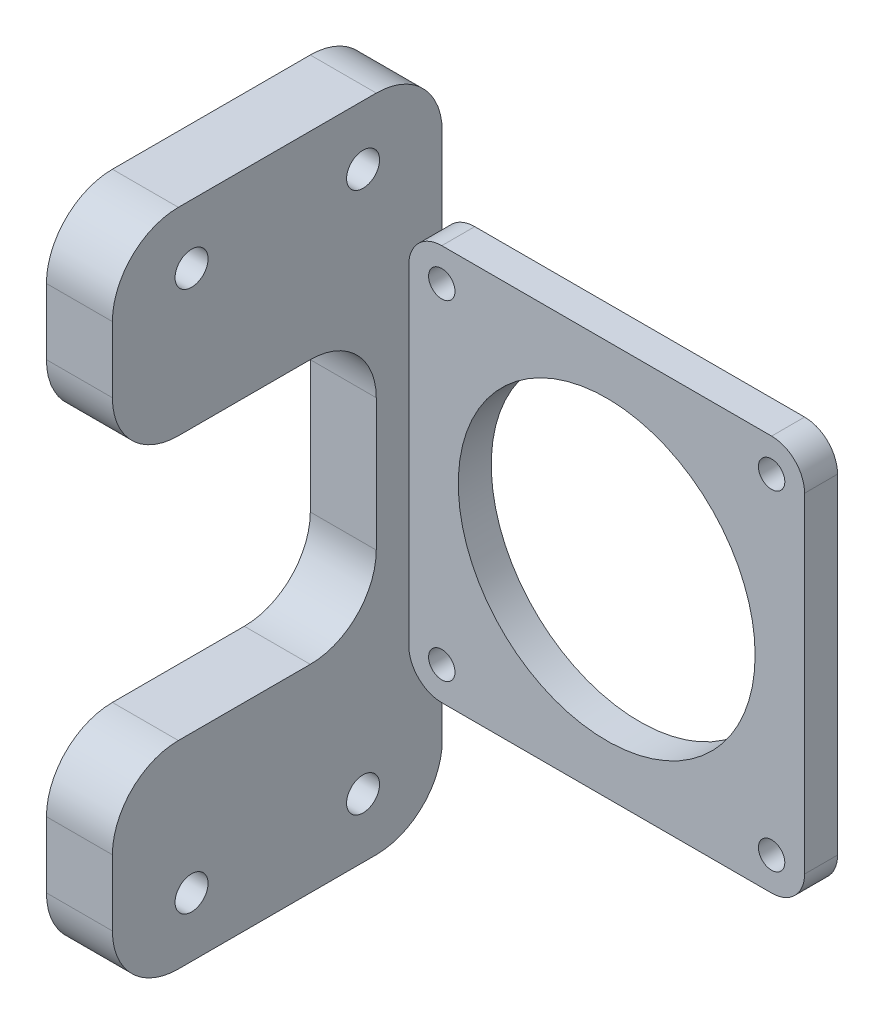
SolidWorks part; units mm, degrees
ref_plane "Front Plane" through (0, 0, 0) normal (0, 0, 1) x (1, 0, 0)
ref_plane "Top Plane" through (0, 0, 0) normal (0, 1, 0) x (1, 0, 0)
ref_plane "Right Plane" through (0, 0, 0) normal (1, 0, 0) x (0, 0, -1)
sketch "Sketch2" plane through (0, 0, 0) normal (0, 0, 1) x (1, 0, 0)
  line L0 (0, 0) -> (0, 35.8787) construction
  line L1 (25, 30) -> (-25, 30)
  line L2 (30, 25) -> (30, -25)
  line L3 (25, -30) -> (-25, -30)
  line L4 (-30, 25) -> (-30, -25)
  line L5 (30, 30) -> (-30, -30) construction
  line L6 (30, -30) -> (-30, 30) construction
  line L7 (-17.179, 0) -> (23.6868, 0) construction
  circle A0 centre (-25, 25) radius 2
  circle A1 centre (25, 25) radius 2
  circle A2 centre (25, -25) radius 2
  circle A3 centre (-25, -25) radius 2
  arc A4 (-25, -30) -> (-30, -25) centre (-25, -25) cw
  arc A5 (30, -25) -> (25, -30) centre (25, -25) cw
  arc A6 (30, 25) -> (25, 30) centre (25, 25) ccw
  arc A7 (-25, 30) -> (-30, 25) centre (-25, 25) ccw
  circle A8 centre (0, 0) radius 22.5
  point P0 (0, 0)
  dimension "D3" = 4
  dimension "D5" = 5
  dimension "D6" = 45
  dimension "D1" = 60
  dimension "D2" = 60
  dimension "D4" = 25
extrude "Boss-Extrude2" add sketch "Sketch2" along normal blind 5
sketch "Sketch3" plane through (-30, 0, 0) normal (-1, 0, 0) x (0, 0, 1)
  line L0 (-22.7369, 0) -> (15.4737, 0) construction
  line L5 (9.9329, 50) -> (39.9329, 50)
  line L6 (-0.0671, 40) -> (-0.0671, -40)
  line L7 (9.9329, -50) -> (39.9329, -50)
  line L8 (49.9329, 40) -> (49.9329, -40)
  line L9 (49.9329, 50) -> (-0.0671, -50) construction
  line L10 (-0.0671, 50) -> (49.9329, -50) construction
  line L11 (24.9329, 0) -> (24.9329, 22.6424) construction
  line L12 (0, 35) -> (68.0193, 35) construction
  line L13 (0, -30) -> (89.451, -30)
  line L14 (19.9329, 20) -> (39.9329, 20)
  line L15 (19.9329, -20) -> (39.9329, -20)
  line L16 (9.9329, 10) -> (9.9329, -10)
  circle A0 centre (11.9329, 41) radius 2.5
  circle A1 centre (37.9329, 41) radius 2.5
  circle A2 centre (37.9329, -41) radius 2.5
  circle A3 centre (11.9329, -41) radius 2.5
  arc A4 (9.9329, -50) -> (-0.0671, -40) centre (9.9329, -40) cw
  arc A5 (39.9329, -50) -> (49.9329, -40) centre (39.9329, -40) ccw
  arc A6 (49.9329, 40) -> (39.9329, 50) centre (39.9329, 40) ccw
  arc A7 (-0.0671, 40) -> (9.9329, 50) centre (9.9329, 40) cw
  arc A8 (49.9329, 30) -> (39.9329, 20) centre (39.9329, 30) cw
  arc A9 (19.9329, -20) -> (9.9329, -10) centre (19.9329, -10) cw
  arc A10 (49.9329, -30) -> (39.9329, -20) centre (39.9329, -30) ccw
  arc A11 (9.9329, 10) -> (19.9329, 20) centre (19.9329, 10) cw
  point P45 (9.9329, -20)
  point P49 (9.9329, 20)
  dimension "D4" = 5
  dimension "D6" = 10
  dimension "D9" = 10
  dimension "D1" = 50
  dimension "D2" = 50
  dimension "D3" = 50
  dimension "D5" = 9
  dimension "D7" = 26
  dimension "D8" = 15
extrude "Boss-Extrude3" add sketch "Sketch3" along normal blind 10
